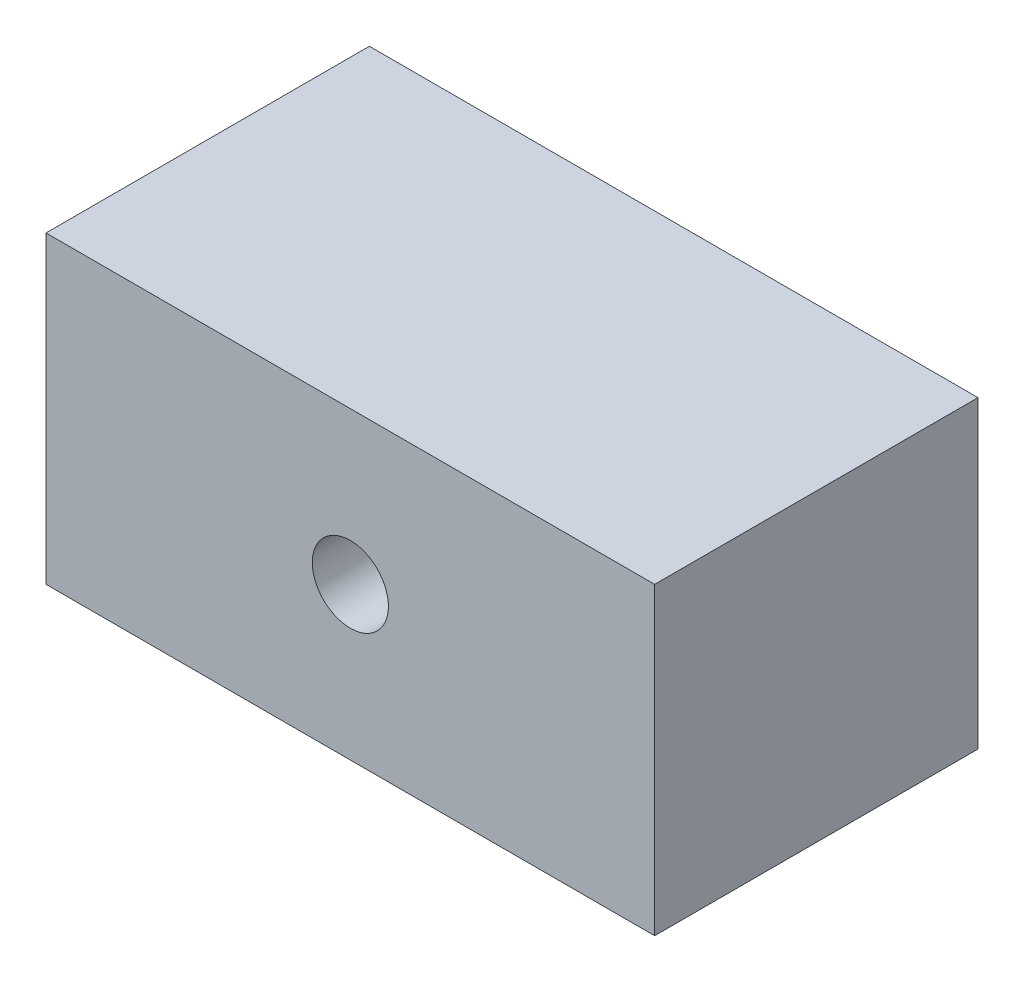
SolidWorks part; units mm, degrees
ref_plane "Front Plane" through (0, 0, 0) normal (0, 0, 1) x (1, 0, 0)
ref_plane "Top Plane" through (0, 0, 0) normal (0, 1, 0) x (1, 0, 0)
ref_plane "Right Plane" through (0, 0, 0) normal (1, 0, 0) x (0, 0, -1)
sketch "Sketch1" plane through (0, 0, 0) normal (0, 0, 1) x (1, 0, 0)
  line L1 (25.4, -12.7) -> (-25.4, -12.7)
  line L2 (25.4, -12.7) -> (25.4, 12.7)
  line L3 (25.4, 12.7) -> (-25.4, 12.7)
  line L4 (-25.4, -12.7) -> (-25.4, 12.7)
  line L5 (25.4, -12.7) -> (-25.4, 12.7) construction
  line L6 (25.4, 12.7) -> (-25.4, -12.7) construction
  point P0 (0, 0)
  dimension "D1" = 50.8
  dimension "D2" = 25.4
extrude "Boss-Extrude1" add sketch "Sketch1" against normal blind 26.9875
hole_wizard "CBORE for #0 Binding Head Machine Screw1" positions "Sketch2" profile "Sketch4" counterbore size "#0" standard "ANSI Inch" end condition through all
sketch "Sketch2" plane through (0, 0, -26.9875) normal (0, 0, -1) x (-1, 0, 0)
  point P0 (0, 0)
sketch "Sketch4" plane through (0, 0, -26.9875) normal (1, 0, 0) x (0, 1, 0)
  line L0 (0, 0) -> (0, 26.9875)
  line L1 (0, 26.9875) -> (3.175, 26.9875)
  line L3 (3.175, 26.9875) -> (3.175, 9.525)
  line L4 (3.175, 9.525) -> (7.9375, 9.525)
  line L5 (7.9375, 9.525) -> (7.9375, 0)
  line L7 (7.9375, 0) -> (0, 0)
  line L11 (0, -6.35) -> (0, 107.95) construction
  dimension "Thru Hole Dia." = 6.35
  dimension "Thru Hole Depth" = 26.9875
  dimension "C'Bore Dia." = 15.875
  dimension "C'Bore Depth" = 9.525
